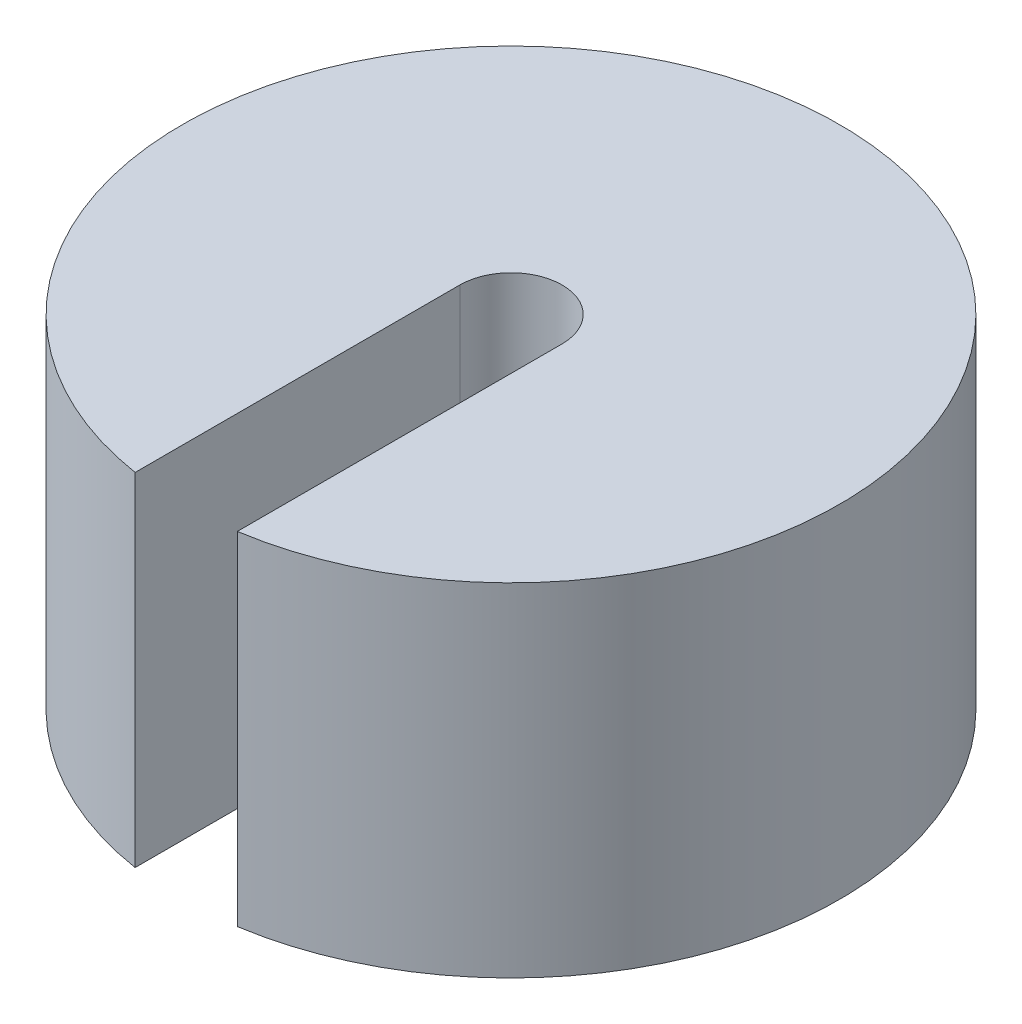
SolidWorks part; units mm, degrees
material "Brass"
ref_plane "Front Plane" through (0, 0, 0) normal (0, 0, 1) x (1, 0, 0)
ref_plane "Top Plane" through (0, 0, 0) normal (0, 1, 0) x (1, 0, 0)
ref_plane "Right Plane" through (0, 0, 0) normal (1, 0, 0) x (0, 0, -1)
sketch "Sketch2" plane through (0, 0, 0) normal (0, 1, 0) x (1, 0, 0)
  circle A0 centre (0, 0) radius 20.75
  dimension "D1" = 41.5
extrude "Boss-Extrude1" add sketch "Sketch2" along normal blind 21.6
sketch "Sketch3" plane through (0, 21.6, 0) normal (0, 1, 0) x (1, 0, 0)
  line L0 (-3.225, 0) -> (-3.225, -21.91)
  line L1 (-3.225, -21.91) -> (3.225, -21.91)
  line L2 (3.225, -21.91) -> (3.225, 0)
  arc A0 (3.225, 0) -> (-3.225, 0) centre (0, 0) ccw
  dimension "D1" = 6.45
  dimension "D2" = 21.91
extrude "Cut-Extrude1" cut sketch "Sketch3" against normal blind 60.6
